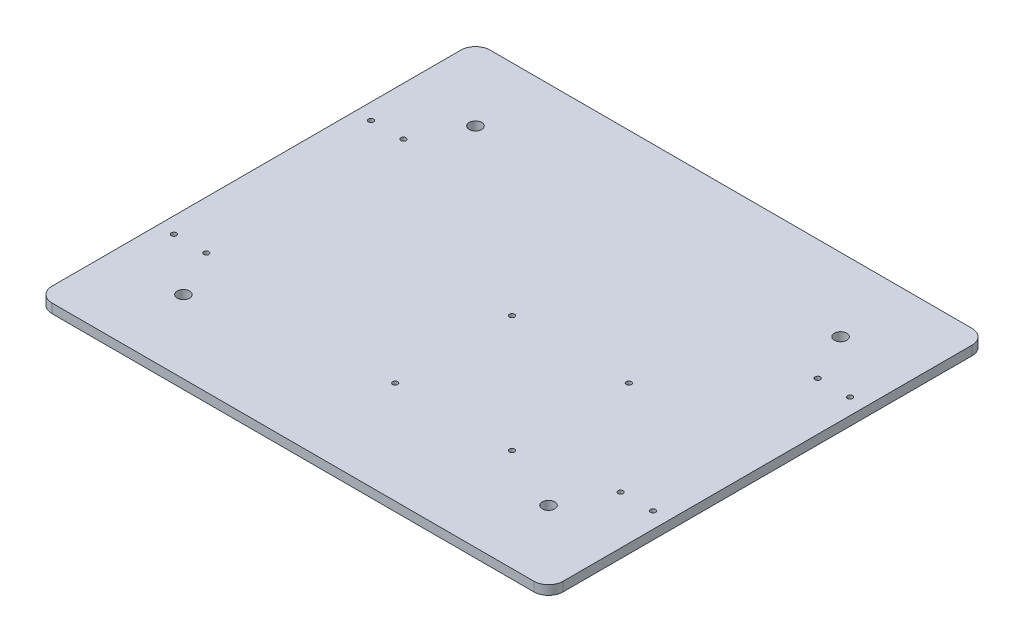
SolidWorks part; units mm, degrees
ref_plane "Front Plane" through (0, 0, 0) normal (0, 0, 1) x (1, 0, 0)
ref_plane "Top Plane" through (0, 0, 0) normal (0, 1, 0) x (1, 0, 0)
ref_plane "Right Plane" through (0, 0, 0) normal (1, 0, 0) x (0, 0, -1)
sketch "Sketch1" plane through (0, 0, 0) normal (0, 1, 0) x (1, 0, 0)
  line L0 (0, 150) -> (0, -150) construction
  line L1 (175, -150) -> (-175, -150)
  line L2 (175, -150) -> (175, 150)
  line L3 (175, 150) -> (-175, 150)
  line L4 (-175, -150) -> (-175, 150)
  line L5 (175, -150) -> (-175, 150) construction
  line L6 (175, 150) -> (-175, -150) construction
  line L7 (-175, 0) -> (175, 0) construction
  point P0 (0, 0)
  dimension "D1" = 350
  dimension "D2" = 300
extrude "Boss-Extrude1" add sketch "Sketch1" along normal blind 6.35
sketch "Sketch2" plane through (0, 0, 0) normal (0, -1, 0) x (1, 0, 0)
  line L0 (175, -150) -> (-175, -150) construction
  line L1 (-175, -150) -> (-175, 150) construction
  circle A0 centre (-125, -100) radius 4.25
  dimension "D3" = 8.5
  dimension "D1" = 50
  dimension "D2" = 50
extrude "Cut-Extrude1" cut sketch "Sketch2" against normal through all
pattern_linear "LPattern2" count 2 spacing 200 along (0, 0, 1) of "Cut-Extrude1"
pattern_linear "LPattern3" count 2 spacing 250 along (1, 0, 0) of "LPattern2", "Cut-Extrude1"
fillet "Fillet1" radius 10 4 edges at (-175, 3.175, 150) (175, 3.175, 150) (175, 3.175, -150) (-175, 3.175, -150)
sketch "Sketch3" plane through (0, 0, 0) normal (0, -1, 0) x (1, 0, 0)
  line L0 (-175, 0) -> (175, 0) construction
  line L1 (-175, -140) -> (-175, 140) construction
  line L2 (175, 140) -> (175, -140) construction
  line L3 (0, -150) -> (0, 150) construction
  line L4 (165, -150) -> (-165, -150) construction
  line L5 (-165, 150) -> (165, 150) construction
sketch "Sketch4" plane through (0, 0, 0) normal (0, -1, 0) x (1, 0, 0)
  circle A0 centre (0, 0) radius 1.75
  dimension "D1" = 3.5
extrude "Cut-Extrude2" cut sketch "Sketch4" against normal through all
pattern_linear "LPattern5" count 2 spacing 80 along (1, 0, 0) count 2 spacing 80 along (0, 0, 1) of "Cut-Extrude2"
sketch "Sketch5" plane through (0, 0, 0) normal (0, -1, 0) x (1, 0, 0)
  line L0 (0, -150) -> (0, 150) construction
  line L1 (-175, 0) -> (175, 0) construction
  circle A0 centre (-141.82, -67.5) radius 1.75
  dimension "D1" = 141.82
  dimension "D2" = 3.5
  dimension "D3" = 67.5
extrude "Cut-Extrude3" cut sketch "Sketch5" against normal through all
pattern_linear "LPattern6" count 2 spacing 22.23 along (-1, 0, 0) count 2 spacing 135 along (0, 0, 1) of "Cut-Extrude3"
sketch "Sketch7" plane through (0, 0, 0) normal (0, -1, 0) x (1, 0, 0)
  line L0 (-175, 0) -> (175, 0) construction
  line L1 (0, -150) -> (0, 150) construction
  circle A0 centre (141.82, -67.5) radius 1.75
  dimension "D1" = 67.5
  dimension "D3" = 3.5
  dimension "D2" = 141.82
extrude "Cut-Extrude4" cut sketch "Sketch7" against normal through all
pattern_linear "LPattern9" count 2 spacing 22.23 along (1, 0, 0) count 2 spacing 135 along (0, 0, 1) of "Cut-Extrude4"
